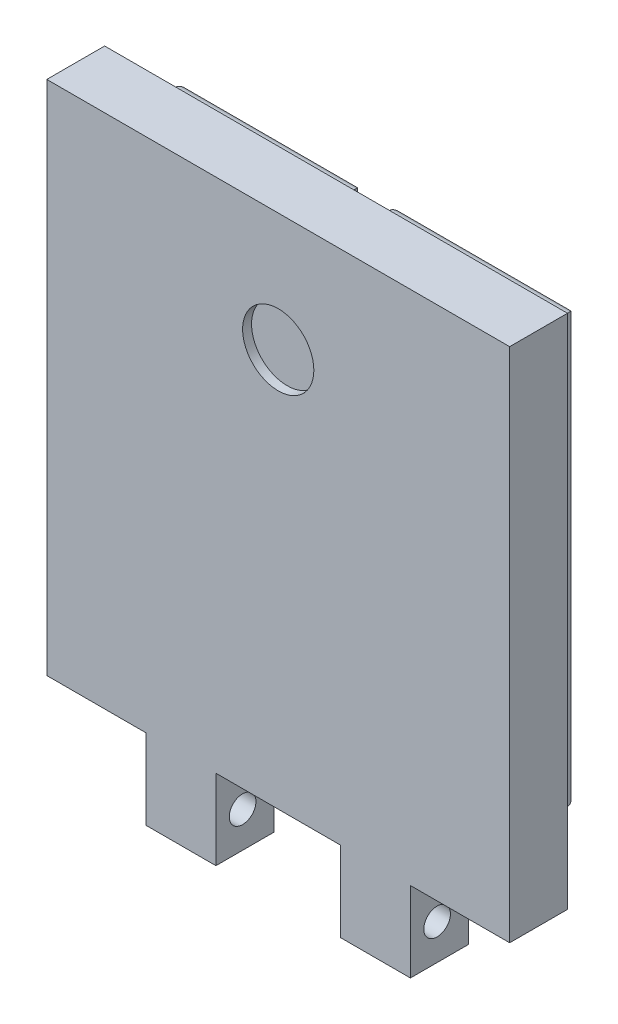
SolidWorks part; units mm, degrees
ref_plane "Front Plane" through (0, 0, 0) normal (0, 0, 1) x (1, 0, 0)
ref_plane "Top Plane" through (0, 0, 0) normal (0, 1, 0) x (1, 0, 0)
ref_plane "Right Plane" through (0, 0, 0) normal (1, 0, 0) x (0, 0, -1)
sketch "Sketch1" plane through (0, 0, 0) normal (0, 0, 1) x (1, 0, 0)
  line L1 (14.85, -33.5) -> (-14.85, -33.5)
  line L2 (14.85, -33.5) -> (14.85, 33.5)
  line L3 (14.85, 33.5) -> (-14.85, 33.5)
  line L4 (-14.85, -33.5) -> (-14.85, 33.5)
  line L5 (14.85, -33.5) -> (-14.85, 33.5) construction
  line L6 (14.85, 33.5) -> (-14.85, -33.5) construction
  point P0 (0, 0)
  dimension "D1" = 29.7
  dimension "D2" = 67
extrude "Boss-Extrude1" add sketch "Sketch1" along normal blind 6
sketch "Sketch2" plane through (14.85, 0, 0) normal (1, 0, 0) x (0, 0, -1)
  line L0 (-3, -33.5) -> (-3, 33.5) construction
  line L1 (-6, -33.5) -> (0, -33.5) construction
  line L2 (-6, 33.5) -> (0, 33.5) construction
  circle A0 centre (-3, -29.5) radius 1.5
  dimension "D1" = 3
  dimension "D2" = 4
extrude "Cut-Extrude1" cut sketch "Sketch2" against normal blind 87
sketch "Sketch3" plane through (0, 33.5, 0) normal (0, 1, 0) x (1, 0, 0)
  line L0 (14.85, 0) -> (-14.85, 0) construction
  line L1 (-21, 0) -> (21, 0)
  line L2 (-21, 0) -> (-21, -6)
  line L3 (-21, -6) -> (21, -6)
  line L4 (21, 0) -> (21, -6)
  point P6 (0, 0)
  point P7 (0, 0)
  dimension "D1" = 42
  dimension "D2" = 0
  dimension "D3" = 6
extrude "Boss-Extrude2" add sketch "Sketch3" against normal blind 58
sketch "Sketch4" plane through (0, 0, 0) normal (0, 0, -1) x (-1, 0, 0)
  line L0 (14.85, -33.5) -> (-14.85, -33.5) construction
  line L1 (-7, -33.5) -> (7, -33.5)
  line L2 (-7, -33.5) -> (-7, -24.5)
  line L3 (-7, -24.5) -> (7, -24.5)
  line L4 (7, -33.5) -> (7, -24.5)
  line L5 (14.85, -24.5) -> (21, -24.5) construction
  dimension "D1" = 7
  dimension "D2" = 7
  dimension "D3" = 0
extrude "Cut-Extrude2" cut sketch "Sketch4" against normal blind 58
sketch "Sketch8" plane through (0, 0, 6) normal (0, 0, 1) x (1, 0, 0)
  line L5 (-26, 33.5) -> (26, 33.5)
  line L6 (-26, 33.5) -> (-26, -24.5)
  line L7 (-26, -24.5) -> (26, -24.5)
  line L8 (26, 33.5) -> (26, -24.5)
  line L16 (7, -24.5) -> (7, -33.5)
  line L17 (7, -33.5) -> (14.85, -33.5)
  line L18 (14.85, -33.5) -> (14.85, -24.5)
  line L19 (14.85, -24.5) -> (21, -24.5)
  line L20 (21, -24.5) -> (21, 33.5)
  line L21 (21, 33.5) -> (-21, 33.5)
  line L22 (-21, 33.5) -> (-21, -24.5)
  line L23 (-21, -24.5) -> (-14.85, -24.5)
  line L24 (-14.85, -24.5) -> (-14.85, -33.5)
  line L25 (-14.85, -33.5) -> (-7, -33.5)
  line L26 (-7, -33.5) -> (-7, -24.5)
  line L27 (-7, -24.5) -> (7, -24.5)
  line L28 (7, -24.5) -> (7, -33.5)
  line L29 (7, -33.5) -> (14.85, -33.5)
  line L30 (14.85, -33.5) -> (14.85, -24.5)
  line L31 (14.85, -24.5) -> (21, -24.5)
  line L32 (21, -24.5) -> (21, 33.5)
  line L33 (21, 33.5) -> (-21, 33.5)
  line L34 (-21, 33.5) -> (-21, -24.5)
  line L35 (-21, -24.5) -> (-14.85, -24.5)
  line L36 (-14.85, -24.5) -> (-14.85, -33.5)
  line L37 (-14.85, -33.5) -> (-7, -33.5)
  line L38 (-7, -33.5) -> (-7, -24.5)
  line L39 (-7, -24.5) -> (7, -24.5)
  line M20 (21, -24.5) -> (21, 33.5)
  line M22 (-21, 33.5) -> (-21, -24.5)
  dimension "D1" = 0
  dimension "D2" = 5
  dimension "D3" = 5
extrude "Boss-Extrude5" add sketch "Sketch8" against normal blind 6 contours L6 L7 L5 M22 | L8 L5 L7 M20
sketch "Sketch5" plane through (0, 0, 0) normal (0, 0, -1) x (-1, 0, 0)
  line L12 (-14.85, -33.5) -> (-7, -33.5)
  line L13 (-7, -33.5) -> (-7, -24.5)
  line L14 (-7, -24.5) -> (7, -24.5)
  line L15 (7, -24.5) -> (7, -33.5)
  line L16 (7, -33.5) -> (14.85, -33.5)
  line L17 (14.85, -33.5) -> (14.85, -24.5)
  line L18 (14.85, -24.5) -> (26, -24.5)
  line L19 (26, -24.5) -> (26, 33.5)
  line L20 (26, 33.5) -> (-26, 33.5)
  line L21 (26, -24.5) -> (26, 33.5)
  line L22 (-26, -24.5) -> (-14.85, -24.5)
  line L23 (-14.85, -24.5) -> (-14.85, -33.5)
  line L24 (-14.85, -33.5) -> (-7, -33.5)
  line L25 (-7, -33.5) -> (-7, -24.5)
  line L26 (-7, -24.5) -> (7, -24.5)
  line L27 (7, -24.5) -> (7, -33.5)
  line L28 (7, -33.5) -> (14.85, -33.5)
  line L29 (14.85, -33.5) -> (14.85, -24.5)
  line L30 (14.85, -24.5) -> (26, -24.5)
  line L32 (26, 33.5) -> (-26, 33.5)
  line L34 (-26, -24.5) -> (-14.85, -24.5)
  line L35 (-14.85, -24.5) -> (-14.85, -33.5)
  line L36 (-26, 33.5) -> (-26, -24.5)
  line L37 (-26, 33.5) -> (-26, -24.5)
  dimension "D1" = 0
extrude "Boss-Extrude3" add sketch "Sketch5" along normal blind 0.5
sketch "Sketch6" plane through (0, 0, -0.5) normal (0, 0, -1) x (-1, 0, 0)
  line L8 (-22, 29.5) -> (-22, -18.5)
  line L9 (-22, -18.5) -> (-18, -18.5)
  line L10 (-18, -18.5) -> (-18, 25.5)
  line L11 (-18, 25.5) -> (-2, 25.5)
  line L12 (-2, 25.5) -> (-2, 29.5)
  line L13 (-2, 29.5) -> (-22, 29.5)
  line L14 (26, 33.5) -> (-26, 33.5) construction
  line L15 (0, 3.3) -> (0, -3.3) construction
  dimension "D1" = 44
  dimension "D2" = 4
  dimension "D3" = 20
  dimension "D4" = 4
  dimension "D5" = 4
  dimension "D6" = 2
extrude "Boss-Extrude4" add sketch "Sketch6" along normal blind 5
fillet "Fillet1" radius 1 6 edges at (2, 27.5, -5.5) (12, 29.5, -5.5) (22, 5.5, -5.5) (20, -18.5, -5.5) (10, 25.5, -5.5) (18, 3.5, -5.5)
mirror "Mirror1" about plane through (0, 0, 0) normal (1, 0, 0) of "Boss-Extrude4", "Fillet1"
sketch "Sketch7" plane through (0, 0, 6) normal (0, 0, 1) x (1, 0, 0)
  circle A0 centre (0, 20.2003) radius 4 construction
  circle A1 centre (0, 20.2003) radius 4
extrude "Cut-Extrude3" cut sketch "Sketch7" against normal blind 1 contours A1
